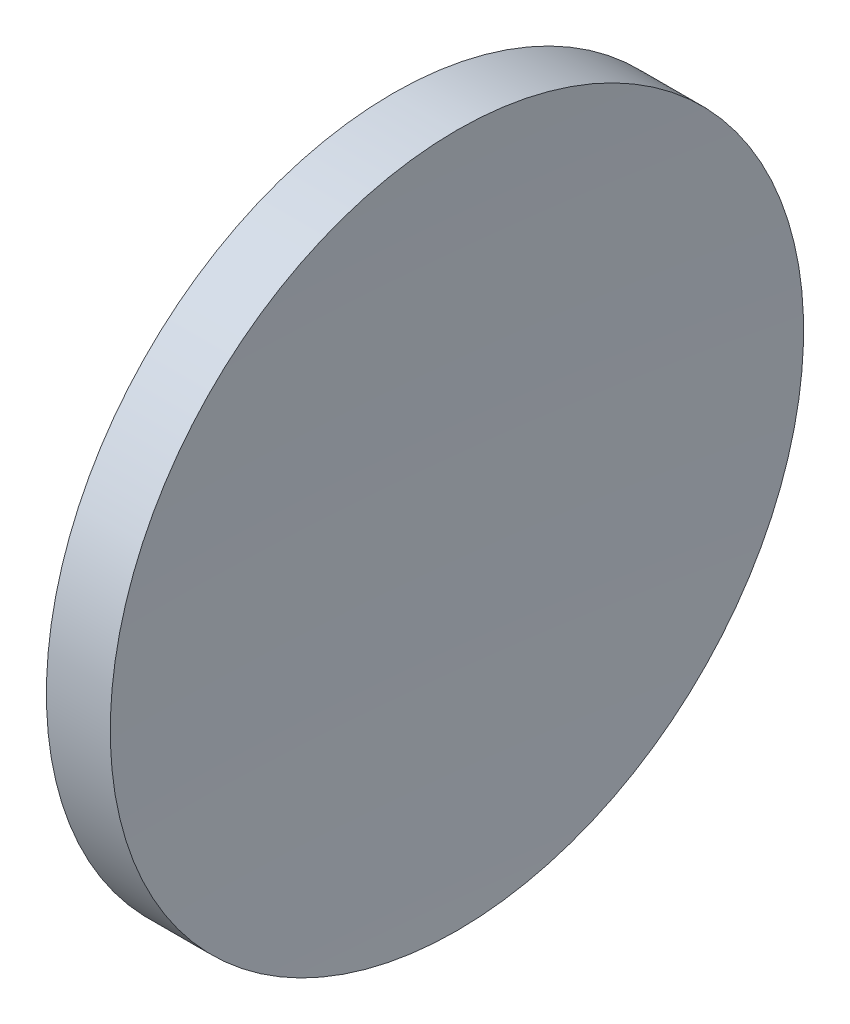
SolidWorks part; units mm, degrees
ref_plane "前视基准面" through (0, 0, 0) normal (0, 0, 1) x (1, 0, 0)
ref_plane "上视基准面" through (0, 0, 0) normal (0, 1, 0) x (1, 0, 0)
ref_plane "右视基准面" through (0, 0, 0) normal (1, 0, 0) x (0, 0, -1)
sketch "草图1" plane through (0, 0, 0) normal (0, 0, 1) x (1, 0, 0)
  line L0 (55.0074, 32.5787) -> (64.0943, 32.5787) construction
  line L1 (57.3582, 32.5787) -> (57.3582, 45.0787)
  line L2 (59.3582, 32.5787) -> (57.3582, 32.5787)
  line L3 (57.3582, 45.0787) -> (59.661, 45.0787)
  arc A0 (59.661, 45.0787) -> (59.3582, 32.5787) centre (317.5382, 32.5787) ccw
revolve "旋转1" add sketch "草图1" angle 360 about L0
